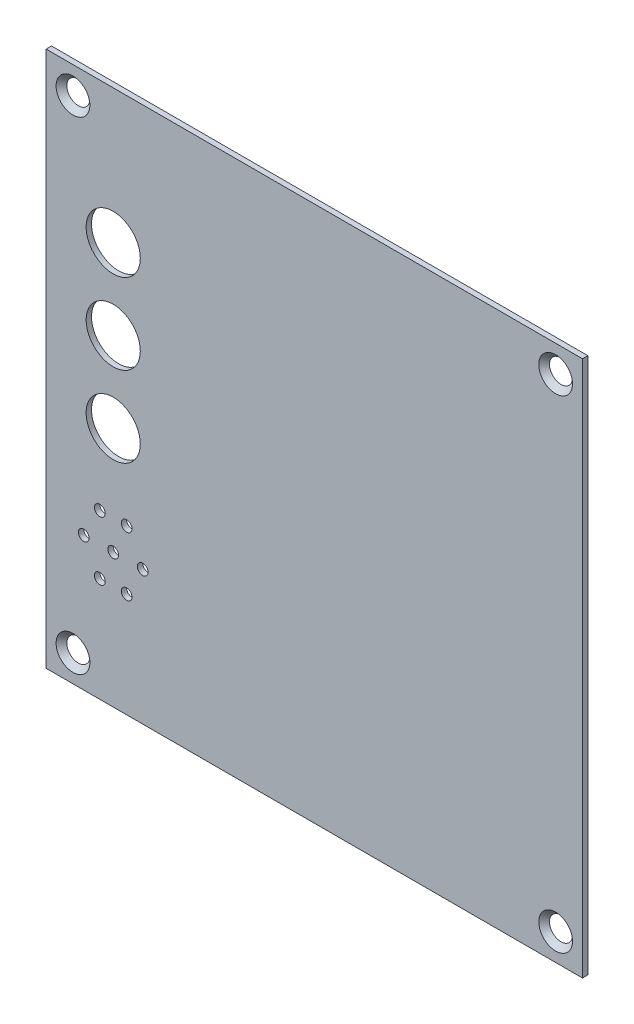
SolidWorks part; units mm, degrees
material "Perspex (TM) Plaque acrylique coulée"
ref_plane "Plan de face" through (0, 0, 0) normal (0, 0, 1) x (1, 0, 0)
ref_plane "Plan de dessus" through (0, 0, 0) normal (0, 1, 0) x (1, 0, 0)
ref_plane "Plan de droite" through (0, 0, 0) normal (1, 0, 0) x (0, 0, -1)
sketch "Esquisse1" plane through (0, 0, 0) normal (0, 0, 1) x (1, 0, 0)
  line L1 (0, 0) -> (100, 0)
  line L2 (0, 0) -> (0, 100)
  line L3 (0, 100) -> (100, 100)
  line L4 (100, 0) -> (100, 100)
  dimension "D1" = 100
  dimension "D2" = 100
extrude "Boss.-Extru.1" add sketch "Esquisse1" along normal blind 1
hole_wizard "Fraisage pour vis à tête fraisée M31" positions "Esquisse3D1" profile "Esquisse3" countersink size "M3" standard "ISO" end condition through all
sketch3d "Esquisse3D1"
  line L0 (100, 100, 1) -> (0, 100, 1) construction
  line L1 (0, 100, 1) -> (0, 0, 1) construction
  line L2 (100, 0, 1) -> (100, 100, 1) construction
  line L3 (0, 0, 1) -> (100, 0, 1) construction
  point P0 (5, 95, 1)
  point P2 (95, 95, 1)
  point P4 (95, 5, 1)
  point P6 (5, 5, 1)
  dimension "D1" = 5
  dimension "D2" = 5
  dimension "D3" = 5
  dimension "D4" = 5
  dimension "D5" = 5
  dimension "D6" = 5
  dimension "D7" = 5
  dimension "D8" = 5
sketch "Esquisse3" plane through (5, 95, 1) normal (1, 0, 0) x (0, -1, 0)
  line L0 (0, 0) -> (0, 1)
  line L1 (0, 1) -> (1.8, 1)
  line L2 (1.8, 1) -> (1.8, 1.35)
  line L3 (1.8, 1.35) -> (3.15, 0)
  line L5 (3.15, 0) -> (0, 0)
  line L6 (-1.8, 1.35) -> (-3.15, 0) construction
  line L11 (0, -6.35) -> (0, 107.95) construction
  dimension "Diamètre du perçage jusqu'au prochain" = 3.6
  dimension "Profondeur du perçage jusqu'au prochain" = 1
  dimension "Diamètre du fraisage entrant" = 6.3
  dimension "Angle du fraisage entrant" = 90
sketch "Esquisse4" plane through (0, 0, 1) normal (0, 0, 1) x (1, 0, 0)
  line L0 (0, 0) -> (100, 0) construction
  line L1 (100, 100) -> (0, 100) construction
  line L2 (0, 100) -> (0, 0) construction
  circle A0 centre (12.5, 75) radius 5.05
  circle A1 centre (12.5, 25) radius 1
  circle A2 centre (10, 19.5) radius 1
  circle A3 centre (7, 25) radius 1
  circle A4 centre (18, 25) radius 1
  circle A5 centre (10, 30.5) radius 1
  circle A6 centre (15, 30.5) radius 1
  circle A7 centre (15, 19.5) radius 1
  circle A8 centre (12.5, 60) radius 5.05
  circle A9 centre (12.5, 45) radius 5.05
  dimension "D3" = 12.5
  dimension "D5" = 18
  dimension "D16" = 12.5
  dimension "D2" = 12.5
  dimension "D4" = 25
  dimension "D6" = 7
  dimension "D7" = 30.5
  dimension "D8" = 19.5
  dimension "D9" = 25
  dimension "D10" = 30.5
  dimension "D11" = 19.5
  dimension "D12" = 10
  dimension "D13" = 5
  dimension "D14" = 10
  dimension "D15" = 5
  dimension "D17" = 12.5
  dimension "D18" = 25
  dimension "D19" = 15
  dimension "D20" = 15
extrude "Enlèv. mat.-Extru.1" cut sketch "Esquisse4" against normal through all
sketch "Esquisse5" plane through (0, 0, 1) normal (0, 0, 1) x (1, 0, 0)
  line L0 (0, 100) -> (0, 0) construction
  line L2 (0, 0) -> (100, 0) construction
  text T0 "Request" font "Century Gothic" height 3.5
  text T1 "Talk Error"
  text T2 "Low batt"
  dimension "D1" = 29
  dimension "D2" = 73
  dimension "D3" = 58
  dimension "D4" = 29
  dimension "D5" = 29
  dimension "D6" = 43
